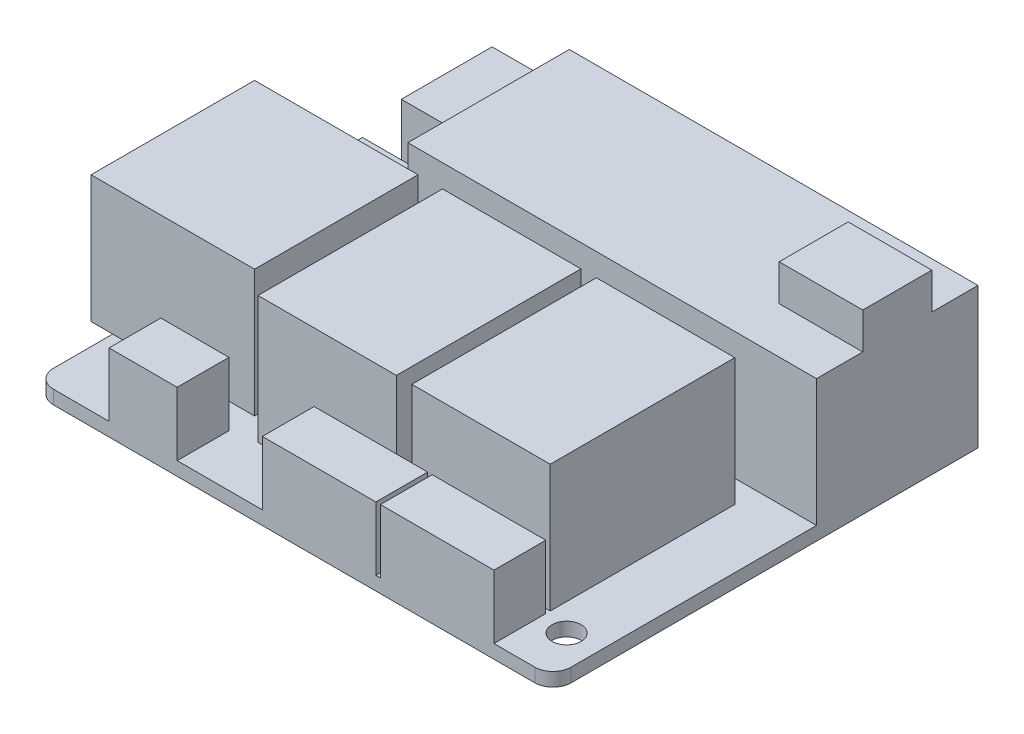
SolidWorks part; units mm, degrees
ref_plane "Front plane" through (0, 0, 0) normal (0, 0, 1) x (1, 0, 0)
ref_plane "Top plane" through (0, 0, 0) normal (0, 1, 0) x (1, 0, 0)
ref_plane "Right Plane" through (0, 0, 0) normal (1, 0, 0) x (0, 0, -1)
sketch "Sketch1" plane through (0, 0, 0) normal (0, 1, 0) x (1, 0, 0)
  line L1 (0, 0) -> (45, 0)
  line L2 (0, 0) -> (0, 17.78)
  line L3 (0, 17.78) -> (45, 17.78)
  line L4 (45, 0) -> (45, 17.78)
  line L5 (38.5, -22.82) -> (23.26, -22.82)
  line L6 (38.5, -22.82) -> (38.5, -2.5)
  line L7 (38.5, -2.5) -> (23.26, -2.5)
  line L8 (23.26, -22.82) -> (23.26, -2.5)
  line L9 (21.56, -22.82) -> (6.32, -22.82)
  line L10 (21.56, -22.82) -> (21.56, -2.5)
  line L11 (21.56, -2.5) -> (6.32, -2.5)
  line L12 (6.32, -22.82) -> (6.32, -2.5)
  line L13 (3.62, -2.5) -> (-14.38, -2.5)
  line L14 (3.62, -2.5) -> (3.62, -20.5)
  line L15 (3.62, -20.5) -> (-14.38, -20.5)
  line L16 (-14.38, -2.5) -> (-14.38, -20.5)
  dimension "D1" = 45
  dimension "D2" = 17.78
  dimension "D3" = 1.7
  dimension "D4" = 2.5
  dimension "D5" = 6.5
  dimension "D6" = 20.32
  dimension "D7" = 15.24
  dimension "D8" = 18
  dimension "D9" = 2.7
extrude "Boss-Extrude1" add sketch "Sketch1" along normal blind 14
sketch "Sketch2" plane through (0, 0, 0) normal (0, 1, 0) x (1, 0, 0)
  line L5 (38.5, -22.82) -> (38.5, -2.5) construction
  line L6 (38.5, -23.32) -> (26, -23.32)
  line L7 (38.5, -23.32) -> (38.5, -29.02)
  line L8 (38.5, -29.02) -> (26, -29.02)
  line L9 (26, -23.32) -> (26, -29.02)
  line L10 (25.5, -23.32) -> (13, -23.32)
  line L11 (25.5, -23.32) -> (25.5, -29.02)
  line L12 (25.5, -29.02) -> (13, -29.02)
  line L13 (13, -23.32) -> (13, -29.02)
  line L14 (23.26, -22.82) -> (38.5, -22.82) construction
  line L36 (3.62, -20.5) -> (3.62, -2.5) construction
  line L37 (3.62, -23.32) -> (-3.88, -23.32)
  line L38 (3.62, -23.32) -> (3.62, -29.02)
  line L39 (3.62, -29.02) -> (-3.88, -29.02)
  line L40 (-3.88, -23.32) -> (-3.88, -29.02)
  dimension "D1" = 5.7
  dimension "D2" = 7.5
  dimension "D3" = 0.5
  dimension "D4" = 12.5
  dimension "D5" = 0.5
extrude "Boss-Extrude2" add sketch "Sketch2" along normal blind 7 separate body
sketch "Sketch4" plane through (0, 0, 0) normal (0, 1, 0) x (1, 0, 0)
  line L0 (0, 17.78) -> (0, 0) construction
  line L1 (-3, 7) -> (-12, 7)
  line L2 (-3, 7) -> (-3, -20.5)
  line L3 (-3, -20.5) -> (-12, -20.5)
  line L4 (-12, 7) -> (-12, -20.5)
  line L8 (-14.38, -20.5) -> (3.62, -20.5) construction
  dimension "D1" = 27.5
  dimension "D2" = 12
  dimension "D3" = 9
extrude "Boss-Extrude4" add sketch "Sketch4" along normal blind 5 separate body
sketch "Sketch5" plane through (0, 0, 0) normal (0, 1, 0) x (1, 0, 0)
  line L1 (-1, 17.78) -> (-8.5, 17.78)
  line L2 (-1, 17.78) -> (-1, 7.78)
  line L3 (-1, 7.78) -> (-8.5, 7.78)
  line L4 (-8.5, 17.78) -> (-8.5, 7.78)
  line L8 (0, 17.78) -> (0, 0) construction
  line L9 (45, 17.78) -> (0, 17.78) construction
  dimension "D1" = 7.5
  dimension "D2" = 10
  dimension "D4" = 1
extrude "Boss-Extrude5" add sketch "Sketch5" along normal blind 10 separate body
sketch "Sketch3" plane through (0, 0, 0) normal (0, 1, 0) x (1, 0, 0)
  line L1 (45, 17.78) -> (-12, 17.78)
  line L2 (45, 17.78) -> (45, -29.02)
  line L3 (45, -29.02) -> (-12, -29.02)
  line L4 (-12, 17.78) -> (-12, -29.02)
  line L8 (-12, 7) -> (-12, -20.5) construction
  line L10 (26, -29.02) -> (38.5, -29.02) construction
  line L11 (45, 17.78) -> (0, 17.78) construction
  line L12 (45, 0) -> (45, 17.78) construction
  line L13 (18.5, 8.48) -> (41.5, 8.48) construction
  circle A0 centre (41.5, -24.02) radius 1.6
  circle A1 centre (41.5, 8.48) radius 1.6
  circle A2 centre (18.5, 8.48) radius 1.6
  dimension "D2" = 3.2
  dimension "D1" = 37.5
  dimension "D3" = 3.5
  dimension "D4" = 23
  dimension "D5" = 5
extrude "Boss-Extrude3" add sketch "Sketch3" against normal blind 1.5
sketch "Sketch6" plane through (0, 14, 0) normal (0, 1, 0) x (1, 0, 0)
  line L0 (45, 0) -> (45, 17.78) construction
  line L1 (45, 12.69) -> (35.8, 12.69)
  line L2 (45, 12.69) -> (45, 5.09)
  line L3 (45, 5.09) -> (35.8, 5.09)
  line L4 (35.8, 12.69) -> (35.8, 5.09)
  line L5 (0, 17.78) -> (0, 0) construction
  point P6 (35.8, 8.89)
  point P9 (0, 8.89)
  dimension "D1" = 7.6
  dimension "D2" = 9.2
extrude "Boss-Extrude6" add sketch "Sketch6" along normal blind 4
fillet "Fillet1" radius 2 3 edges at (45, -0.75, 29.02) (-12, -0.75, 29.02) (-12, -0.75, -17.78)
